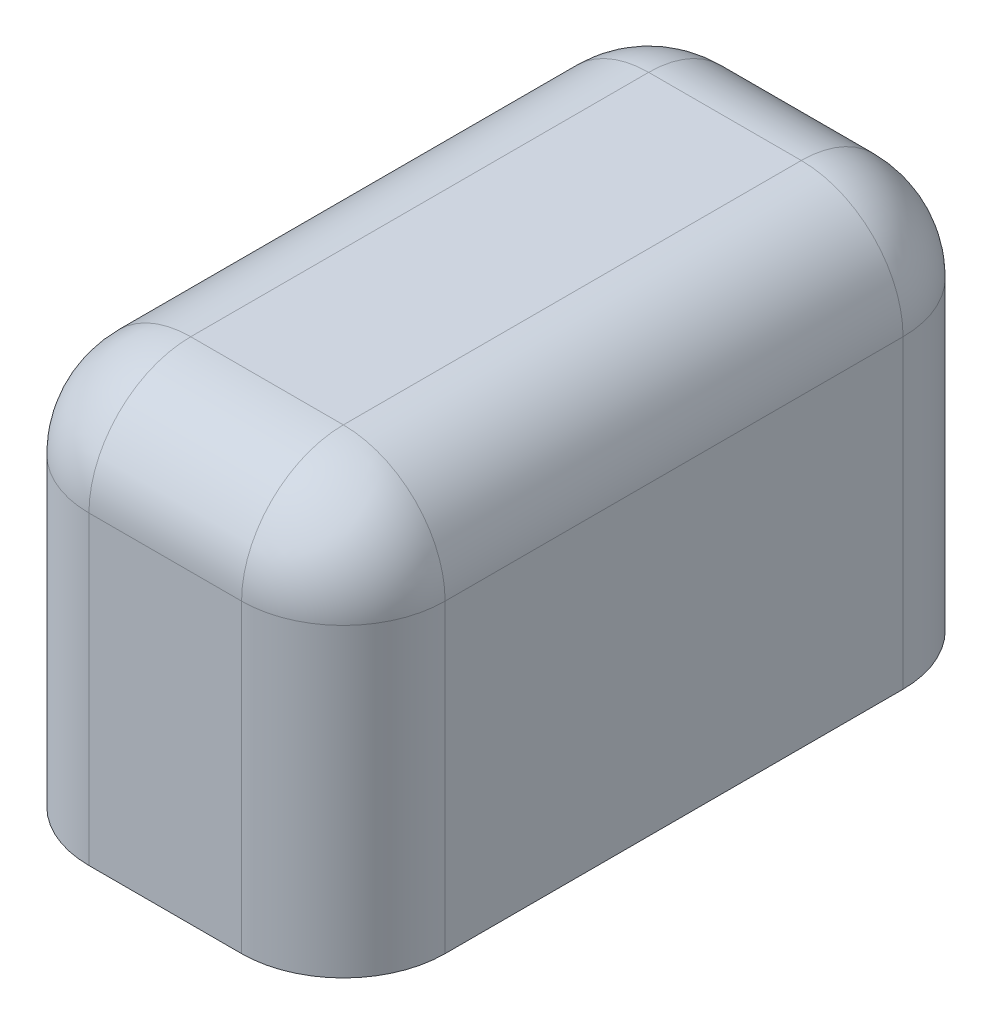
SolidWorks part; units mm, degrees
ref_plane "Front Plane" through (0, 0, 0) normal (0, 0, 1) x (1, 0, 0)
ref_plane "Top Plane" through (0, 0, 0) normal (0, 1, 0) x (1, 0, 0)
ref_plane "Right Plane" through (0, 0, 0) normal (1, 0, 0) x (0, 0, -1)
sketch "Sketch1" plane through (0, 0, 0) normal (1, 0, 0) x (0, 0, -1)
  line L1 (0, 0) -> (16.51, 0)
  line L2 (0, 0) -> (0, 10.16)
  line L3 (0, 10.16) -> (16.51, 10.16)
  line L4 (16.51, 0) -> (16.51, 10.16)
  dimension "D1" = 10.16
  dimension "D2" = 16.51
extrude "Boss-Extrude1" add sketch "Sketch1" along normal mid plane 8.89
fillet "Fillet1" radius 2.54 8 edges at (0, 10.16, -16.51) (-4.445, 10.16, -8.255) (0, 10.16, 0) (4.445, 10.16, -8.255) (4.445, 5.08, -16.51) (-4.445, 5.08, -16.51) (-4.445, 5.08, 0) (4.445, 5.08, 0)
move or copy body "Body-Move/Copy1" [suppressed] bodies to move or copy 101 parameters "D1"=0, "D2"=0, "D3"=0
